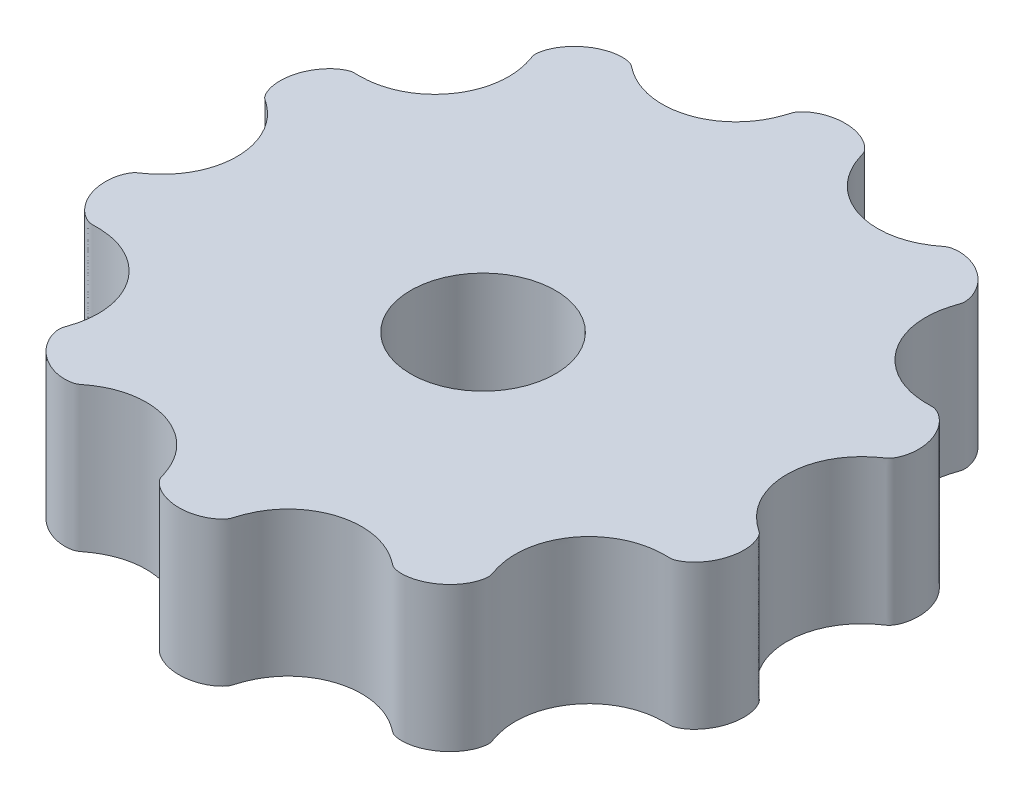
SolidWorks part; units mm, degrees
ref_plane "Front Plane" through (0, 0, 0) normal (0, 0, 1) x (1, 0, 0)
ref_plane "Top Plane" through (0, 0, 0) normal (0, 1, 0) x (1, 0, 0)
ref_plane "Right Plane" through (0, 0, 0) normal (1, 0, 0) x (0, 0, -1)
sketch "Sketch2" plane through (0, 0, 0) normal (0, 1, 0) x (1, 0, 0)
  line L0 (15.6249, 0) -> (-15.6249, 0) construction
  spline S0 degree 4 poles (10.8627, -2.3489) (10.8548, -2.3356) (10.8383, -2.3095) (10.8118, -2.2714) (10.77, -2.2253) (10.7092, -2.1837) (10.6403, -2.1348) (10.5624, -2.0782) (10.4776, -2.012) (10.3744, -1.9255) (10.2561, -1.8157) (10.1267, -1.6784) (9.9922, -1.5103) (9.8721, -1.331) (9.7674, -1.1432) (9.6789, -0.9459) (9.6073, -0.7442) (9.5599, -0.5592) (9.5304, -0.4045) (9.5133, -0.2645) (9.5042, -0.1702) (9.4997, -0.039) (9.4996, 0.0348) (9.5038, 0.1621) (9.5121, 0.2517) (9.5245, 0.3605) (9.5411, 0.4582) (9.5668, 0.5857) (9.6065, 0.7361) (9.6655, 0.9121) (9.75, 1.1075) (9.852, 1.2979) (9.9694, 1.4785) (10.1013, 1.6488) (10.2284, 1.7876) (10.3448, 1.8989) (10.4463, 1.9865) (10.5197, 2.0451) (10.5838, 2.0937) (10.641, 2.1349) (10.6898, 2.1706) (10.7437, 2.2055) (10.7951, 2.2496) (10.8403, 2.311) (10.8841, 2.3827) (10.9343, 2.4894) (11.0002, 2.6876) (11.0407, 2.9778) (11.0115, 3.3556) (10.8743, 3.7728) (10.6723, 4.0946) (10.4644, 4.3047) (10.2934, 4.4229) (10.1936, 4.4756) (10.1202, 4.505) (10.0528, 4.5253) (9.992, 4.5302) (9.9188, 4.5272) (9.8337, 4.5273) (9.7361, 4.5276) (9.6266, 4.5327) (9.5172, 4.5414) (9.4083, 4.5547) (9.2729, 4.5766) (9.1119, 4.6118) (8.9272, 4.666) (8.722, 4.7456) (8.5243, 4.8426) (8.288, 4.9849) (8.0252, 5.1877) (7.758, 5.4641) (7.5129, 5.8251) (7.3343, 6.2184) (7.2385, 6.5803) (7.2002, 6.898) (7.1976, 7.1627) (7.2125, 7.3724) (7.2437, 7.5789) (7.2844, 7.7559) (7.3244, 7.8928) (7.3569, 7.9913) (7.3774, 8.053) (7.3956, 8.102) (7.4112, 8.1658) (7.4126, 8.2693) (7.3936, 8.4084) (7.3248, 8.6324) (7.174, 8.9091) (6.9645, 9.1518) (6.709, 9.3505) (6.4711, 9.4808) (6.2666, 9.5615) (6.0593, 9.6132) (5.8773, 9.6322) (5.725, 9.6284) (5.6081, 9.6108) (5.5203, 9.5887) (5.4392, 9.5544) (5.3742, 9.5002) (5.2792, 9.4314) (5.1556, 9.3435) (4.9977, 9.2467) (4.8029, 9.1463) (4.6002, 9.0629) (4.3912, 8.9964) (4.1772, 8.9481) (3.9597, 8.9181) (3.7403, 8.9069) (3.4104, 8.9186) (3.0342, 8.9868) (2.6266, 9.1359) (2.2143, 9.3876) (1.8947, 9.6642) (1.6607, 9.946) (1.4966, 10.2081) (1.3849, 10.435) (1.3198, 10.5945) (1.2718, 10.7345) (1.2347, 10.8518) (1.2083, 10.949) (1.1472, 11.0306) (1.0807, 11.1054) (1.004, 11.1722) (0.9232, 11.2326) (0.8141, 11.3007) (0.6749, 11.3701) (0.4536, 11.4511) (0.1862, 11.5013) (-0.0944, 11.508) (-0.3799, 11.4665) (-0.6145, 11.3979) (-0.8222, 11.3016) (-0.9804, 11.1957) (-1.0932, 11.0938) (-1.1632, 11.0103) (-1.2092, 10.9408) (-1.2362, 10.8468) (-1.2643, 10.7588) (-1.2935, 10.6703) (-1.3324, 10.5659) (-1.3833, 10.4408) (-1.4592, 10.2808) (-1.5685, 10.0906) (-1.7084, 9.8921) (-1.8668, 9.7071) (-2.0427, 9.5374) (-2.2827, 9.3465) (-2.5882, 9.162) (-2.9131, 9.029) (-3.2473, 8.9481) (-3.5205, 8.9147) (-3.7403, 8.9069) (-3.9597, 8.9181) (-4.1772, 8.9481) (-4.3912, 8.9964) (-4.6002, 9.0629) (-4.8029, 9.1463) (-4.9977, 9.2467) (-5.1556, 9.3435) (-5.2792, 9.4314) (-5.3742, 9.5002) (-5.4392, 9.5544) (-5.5203, 9.5887) (-5.6081, 9.6108) (-5.725, 9.6284) (-5.8773, 9.6322) (-6.0593, 9.6132) (-6.2666, 9.5615) (-6.4711, 9.4808) (-6.7091, 9.3504) (-6.9645, 9.1518) (-7.174, 8.9091) (-7.3247, 8.6324) (-7.3936, 8.4084) (-7.4125, 8.2694) (-7.4114, 8.1658) (-7.3921, 8.0895) (-7.3642, 8.0164) (-7.3286, 7.9051) (-7.2841, 7.756) (-7.2439, 7.5789) (-7.2124, 7.3724) (-7.1976, 7.1627) (-7.2002, 6.898) (-7.2385, 6.5803) (-7.3343, 6.2184) (-7.513, 5.8251) (-7.789, 5.4184) (-8.1046, 5.1102) (-8.425, 4.8913) (-8.722, 4.7456) (-8.9272, 4.666) (-9.1119, 4.6118) (-9.2729, 4.5766) (-9.4083, 4.5547) (-9.5172, 4.5414) (-9.6266, 4.5327) (-9.7361, 4.5276) (-9.8337, 4.5273) (-9.9188, 4.5272) (-9.992, 4.5302) (-10.0528, 4.5253) (-10.1202, 4.5049) (-10.1936, 4.4756) (-10.2934, 4.4228) (-10.419, 4.3361) (-10.5552, 4.2128) (-10.728, 4.006) (-10.8917, 3.72) (-11.0115, 3.3557) (-11.0407, 2.9777) (-11.0002, 2.6876) (-10.9343, 2.4894) (-10.8841, 2.3827) (-10.8403, 2.311) (-10.7951, 2.2496) (-10.7437, 2.2055) (-10.6898, 2.1706) (-10.641, 2.1349) (-10.5838, 2.0937) (-10.5197, 2.0451) (-10.4463, 1.9865) (-10.3448, 1.8989) (-10.2284, 1.7876) (-10.1013, 1.6488) (-9.9694, 1.4785) (-9.852, 1.2979) (-9.75, 1.1075) (-9.6655, 0.912) (-9.5983, 0.7119) (-9.5545, 0.5357) (-9.5276, 0.3828) (-9.5121, 0.2572) (-9.5038, 0.1544) (-9.4985, 0.0087) (-9.5005, -0.0802) (-9.5099, -0.2587) (-9.5304, -0.3927) (-9.5599, -0.5672) (-9.6073, -0.7393) (-9.6789, -0.9488) (-9.7674, -1.1415) (-9.8721, -1.3321) (-9.9922, -1.5096) (-10.1267, -1.6789) (-10.2561, -1.8154) (-10.3744, -1.9257) (-10.4776, -2.0119) (-10.5624, -2.0782) (-10.6403, -2.1347) (-10.7092, -2.1837) (-10.77, -2.2253) (-10.8118, -2.2714) (-10.8383, -2.3095) (-10.8548, -2.3356) (-10.8627, -2.3489) knots 0 0 0 0 0 0.001333 0.002666 0.003999 0.005332 0.007653 0.009974 0.012295 0.014616 0.019258 0.0239 0.028542 0.033183 0.037824 0.042465 0.047106 0.051747 0.054067 0.056388 0.058708 0.061029 0.063242 0.065455 0.067668 0.069881 0.072094 0.074307 0.078733 0.083382 0.08803 0.092679 0.097328 0.101956 0.106583 0.108896 0.11121 0.113524 0.114681 0.115837 0.117292 0.118746 0.1202 0.121654 0.123827 0.126 0.130347 0.13962 0.148891 0.15838 0.167867 0.172067 0.174166 0.176266 0.177578 0.17889 0.180201 0.181513 0.183879 0.186244 0.18861 0.190975 0.193341 0.195706 0.200437 0.205181 0.209925 0.21467 0.219414 0.228944 0.238475 0.24767 0.256866 0.266034 0.270619 0.275203 0.279676 0.284148 0.288621 0.290858 0.291976 0.293094 0.294227 0.29536 0.297625 0.301964 0.306302 0.31546 0.324616 0.329345 0.334073 0.338802 0.34353 0.347716 0.349809 0.351902 0.353711 0.35552 0.357329 0.359138 0.363859 0.368579 0.373299 0.378019 0.382748 0.387476 0.392204 0.396932 0.401678 0.415915 0.425003 0.434092 0.443153 0.452214 0.45646 0.460705 0.464951 0.467074 0.469196 0.471363 0.47353 0.475711 0.477892 0.480073 0.482254 0.486775 0.491297 0.500341 0.505595 0.510849 0.516103 0.521357 0.525258 0.527209 0.52916 0.530763 0.532367 0.535573 0.537176 0.538779 0.541986 0.547215 0.552445 0.557674 0.562903 0.568199 0.573494 0.584085 0.593577 0.598322 0.603068 0.607796 0.612524 0.617252 0.621981 0.626701 0.631421 0.636141 0.640862 0.642671 0.64448 0.646289 0.648098 0.650191 0.652284 0.65647 0.661198 0.665927 0.670655 0.675384 0.68454 0.693698 0.698036 0.702375 0.70464 0.705773 0.706906 0.709142 0.711379 0.715852 0.720324 0.724797 0.729381 0.733966 0.743134 0.75233 0.761525 0.771056 0.78533 0.790075 0.794819 0.799563 0.804294 0.806659 0.809025 0.81139 0.813756 0.816121 0.818487 0.819799 0.82111 0.822422 0.823734 0.825834 0.827933 0.832133 0.836876 0.84162 0.851109 0.86038 0.869653 0.874 0.876173 0.878346 0.8798 0.881254 0.882708 0.884163 0.885319 0.886476 0.88879 0.891104 0.893417 0.898044 0.902672 0.907321 0.91197 0.916618 0.921267 0.925693 0.930119 0.932332 0.934545 0.936758 0.938971 0.943612 0.945933 0.948253 0.952894 0.957535 0.962176 0.966817 0.971458 0.9761 0.980742 0.985384 0.987705 0.990026 0.992347 0.994668 0.996001 0.997334 0.998667 1 1 1 1 1 construction
  spline S1 degree 4 poles (9.5, 0) (9.5, 0.0225) (9.5007, 0.0678) (9.5038, 0.1621) (9.5121, 0.2517) (9.5245, 0.3605) (9.5411, 0.4582) (9.5668, 0.5857) (9.6065, 0.7361) (9.6655, 0.9121) (9.75, 1.1075) (9.852, 1.2979) (9.9694, 1.4785) (10.1013, 1.6488) (10.2284, 1.7876) (10.3448, 1.8989) (10.4463, 1.9865) (10.5197, 2.0451) (10.5838, 2.0937) (10.641, 2.1349) (10.6898, 2.1706) (10.7437, 2.2055) (10.7951, 2.2496) (10.8403, 2.311) (10.8841, 2.3827) (10.9343, 2.4894) (11.0002, 2.6876) (11.0407, 2.9778) (11.0115, 3.3556) (10.8743, 3.7728) (10.6723, 4.0946) (10.4644, 4.3047) (10.2934, 4.4229) (10.1936, 4.4756) (10.1202, 4.505) (10.0528, 4.5253) (9.992, 4.5302) (9.9188, 4.5272) (9.8337, 4.5273) (9.7361, 4.5276) (9.6266, 4.5327) (9.5172, 4.5414) (9.4083, 4.5547) (9.2729, 4.5766) (9.1119, 4.6118) (8.9272, 4.666) (8.722, 4.7456) (8.5243, 4.8426) (8.288, 4.9849) (8.0252, 5.1877) (7.758, 5.4641) (7.5129, 5.8251) (7.3343, 6.2184) (7.2385, 6.5803) (7.2002, 6.898) (7.1976, 7.1627) (7.2125, 7.3724) (7.2437, 7.5789) (7.2844, 7.7559) (7.3244, 7.8928) (7.3569, 7.9913) (7.3774, 8.053) (7.3956, 8.102) (7.4112, 8.1658) (7.4126, 8.2693) (7.3936, 8.4084) (7.3248, 8.6324) (7.174, 8.9091) (6.9645, 9.1518) (6.709, 9.3505) (6.4711, 9.4808) (6.2666, 9.5615) (6.0593, 9.6132) (5.8773, 9.6322) (5.725, 9.6284) (5.6081, 9.6108) (5.5203, 9.5887) (5.4392, 9.5544) (5.3742, 9.5002) (5.2792, 9.4314) (5.1556, 9.3435) (4.9977, 9.2467) (4.8029, 9.1463) (4.6002, 9.0629) (4.3912, 8.9964) (4.1772, 8.9481) (3.9597, 8.9181) (3.7403, 8.9069) (3.4104, 8.9186) (3.0342, 8.9868) (2.6266, 9.1359) (2.2143, 9.3876) (1.8947, 9.6642) (1.6607, 9.946) (1.4966, 10.2081) (1.3849, 10.435) (1.3198, 10.5945) (1.2718, 10.7345) (1.2347, 10.8518) (1.2083, 10.949) (1.1472, 11.0306) (1.0807, 11.1054) (1.004, 11.1722) (0.9232, 11.2326) (0.8141, 11.3007) (0.6749, 11.3701) (0.4536, 11.4511) (0.1862, 11.5013) (-0.0944, 11.508) (-0.3799, 11.4665) (-0.6145, 11.3979) (-0.8222, 11.3016) (-0.9804, 11.1957) (-1.0932, 11.0938) (-1.1632, 11.0103) (-1.2092, 10.9408) (-1.2362, 10.8468) (-1.2643, 10.7588) (-1.2935, 10.6703) (-1.3324, 10.5659) (-1.3833, 10.4408) (-1.4592, 10.2808) (-1.5685, 10.0906) (-1.7084, 9.8921) (-1.8668, 9.7071) (-2.0427, 9.5374) (-2.2827, 9.3465) (-2.5882, 9.162) (-2.9131, 9.029) (-3.2473, 8.9481) (-3.5205, 8.9147) (-3.7403, 8.9069) (-3.9597, 8.9181) (-4.1772, 8.9481) (-4.3912, 8.9964) (-4.6002, 9.0629) (-4.8029, 9.1463) (-4.9977, 9.2467) (-5.1556, 9.3435) (-5.2792, 9.4314) (-5.3742, 9.5002) (-5.4392, 9.5544) (-5.5203, 9.5887) (-5.6081, 9.6108) (-5.725, 9.6284) (-5.8773, 9.6322) (-6.0593, 9.6132) (-6.2666, 9.5615) (-6.4711, 9.4808) (-6.7091, 9.3504) (-6.9645, 9.1518) (-7.174, 8.9091) (-7.3247, 8.6324) (-7.3936, 8.4084) (-7.4125, 8.2694) (-7.4114, 8.1658) (-7.3921, 8.0895) (-7.3642, 8.0164) (-7.3286, 7.9051) (-7.2841, 7.756) (-7.2439, 7.5789) (-7.2124, 7.3724) (-7.1976, 7.1627) (-7.2002, 6.898) (-7.2385, 6.5803) (-7.3343, 6.2184) (-7.513, 5.8251) (-7.789, 5.4184) (-8.1046, 5.1102) (-8.425, 4.8913) (-8.722, 4.7456) (-8.9272, 4.666) (-9.1119, 4.6118) (-9.2729, 4.5766) (-9.4083, 4.5547) (-9.5172, 4.5414) (-9.6266, 4.5327) (-9.7361, 4.5276) (-9.8337, 4.5273) (-9.9188, 4.5272) (-9.992, 4.5302) (-10.0528, 4.5253) (-10.1202, 4.5049) (-10.1936, 4.4756) (-10.2934, 4.4228) (-10.419, 4.3361) (-10.5552, 4.2128) (-10.728, 4.006) (-10.8917, 3.72) (-11.0115, 3.3557) (-11.0407, 2.9777) (-11.0002, 2.6876) (-10.9343, 2.4894) (-10.8841, 2.3827) (-10.8403, 2.311) (-10.7951, 2.2496) (-10.7437, 2.2055) (-10.6898, 2.1706) (-10.641, 2.1349) (-10.5838, 2.0937) (-10.5197, 2.0451) (-10.4463, 1.9865) (-10.3448, 1.8989) (-10.2284, 1.7876) (-10.1013, 1.6488) (-9.9694, 1.4785) (-9.852, 1.2979) (-9.75, 1.1075) (-9.6655, 0.912) (-9.5983, 0.7119) (-9.5545, 0.5357) (-9.5276, 0.3828) (-9.5121, 0.2572) (-9.5038, 0.1544) (-9.5007, 0.0686) (-9.5, 0.0225) (-9.5, 0) knots 0.061029 0.061029 0.061029 0.061029 0.061029 0.063242 0.065455 0.067668 0.069881 0.072094 0.074307 0.078733 0.083382 0.08803 0.092679 0.097328 0.101956 0.106583 0.108896 0.11121 0.113524 0.114681 0.115837 0.117292 0.118746 0.1202 0.121654 0.123827 0.126 0.130347 0.13962 0.148891 0.15838 0.167867 0.172067 0.174166 0.176266 0.177578 0.17889 0.180201 0.181513 0.183879 0.186244 0.18861 0.190975 0.193341 0.195706 0.200437 0.205181 0.209925 0.21467 0.219414 0.228944 0.238475 0.24767 0.256866 0.266034 0.270619 0.275203 0.279676 0.284148 0.288621 0.290858 0.291976 0.293094 0.294227 0.29536 0.297625 0.301964 0.306302 0.31546 0.324616 0.329345 0.334073 0.338802 0.34353 0.347716 0.349809 0.351902 0.353711 0.35552 0.357329 0.359138 0.363859 0.368579 0.373299 0.378019 0.382748 0.387476 0.392204 0.396932 0.401678 0.415915 0.425003 0.434092 0.443153 0.452214 0.45646 0.460705 0.464951 0.467074 0.469196 0.471363 0.47353 0.475711 0.477892 0.480073 0.482254 0.486775 0.491297 0.500341 0.505595 0.510849 0.516103 0.521357 0.525258 0.527209 0.52916 0.530763 0.532367 0.535573 0.537176 0.538779 0.541986 0.547215 0.552445 0.557674 0.562903 0.568199 0.573494 0.584085 0.593577 0.598322 0.603068 0.607796 0.612524 0.617252 0.621981 0.626701 0.631421 0.636141 0.640862 0.642671 0.64448 0.646289 0.648098 0.650191 0.652284 0.65647 0.661198 0.665927 0.670655 0.675384 0.68454 0.693698 0.698036 0.702375 0.70464 0.705773 0.706906 0.709142 0.711379 0.715852 0.720324 0.724797 0.729381 0.733966 0.743134 0.75233 0.761525 0.771056 0.78533 0.790075 0.794819 0.799563 0.804294 0.806659 0.809025 0.81139 0.813756 0.816121 0.818487 0.819799 0.82111 0.822422 0.823734 0.825834 0.827933 0.832133 0.836876 0.84162 0.851109 0.86038 0.869653 0.874 0.876173 0.878346 0.8798 0.881254 0.882708 0.884163 0.885319 0.886476 0.88879 0.891104 0.893417 0.898044 0.902672 0.907321 0.91197 0.916618 0.921267 0.925693 0.930119 0.932332 0.934545 0.936758 0.938971 0.938971 0.938971 0.938971 0.938971 construction
  spline S2 degree 4 poles (10.8627, 2.3489) (10.8548, 2.3356) (10.8383, 2.3095) (10.8118, 2.2714) (10.77, 2.2253) (10.7092, 2.1837) (10.6403, 2.1348) (10.5624, 2.0782) (10.4776, 2.012) (10.3744, 1.9255) (10.2561, 1.8157) (10.1267, 1.6784) (9.9922, 1.5103) (9.8721, 1.331) (9.7674, 1.1432) (9.6789, 0.9459) (9.6073, 0.7442) (9.5599, 0.5592) (9.5304, 0.4045) (9.5133, 0.2645) (9.5042, 0.1702) (9.4997, 0.039) (9.4996, -0.0348) (9.5038, -0.1621) (9.5121, -0.2517) (9.5245, -0.3605) (9.5411, -0.4582) (9.5668, -0.5857) (9.6065, -0.7361) (9.6655, -0.9121) (9.75, -1.1075) (9.852, -1.2979) (9.9694, -1.4785) (10.1013, -1.6488) (10.2284, -1.7876) (10.3448, -1.8989) (10.4463, -1.9865) (10.5197, -2.0451) (10.5838, -2.0937) (10.641, -2.1349) (10.6898, -2.1706) (10.7437, -2.2055) (10.7951, -2.2496) (10.8403, -2.311) (10.8841, -2.3827) (10.9343, -2.4894) (11.0002, -2.6876) (11.0407, -2.9778) (11.0115, -3.3556) (10.8743, -3.7728) (10.6723, -4.0946) (10.4644, -4.3047) (10.2934, -4.4229) (10.1936, -4.4756) (10.1202, -4.505) (10.0528, -4.5253) (9.992, -4.5302) (9.9188, -4.5272) (9.8337, -4.5273) (9.7361, -4.5276) (9.6266, -4.5327) (9.5172, -4.5414) (9.4083, -4.5547) (9.2729, -4.5766) (9.1119, -4.6118) (8.9272, -4.666) (8.722, -4.7456) (8.5243, -4.8426) (8.288, -4.9849) (8.0252, -5.1877) (7.758, -5.4641) (7.5129, -5.8251) (7.3343, -6.2184) (7.2385, -6.5803) (7.2002, -6.898) (7.1976, -7.1627) (7.2125, -7.3724) (7.2437, -7.5789) (7.2844, -7.7559) (7.3244, -7.8928) (7.3569, -7.9913) (7.3774, -8.053) (7.3956, -8.102) (7.4112, -8.1658) (7.4126, -8.2693) (7.3936, -8.4084) (7.3248, -8.6324) (7.174, -8.9091) (6.9645, -9.1518) (6.709, -9.3505) (6.4711, -9.4808) (6.2666, -9.5615) (6.0593, -9.6132) (5.8773, -9.6322) (5.725, -9.6284) (5.6081, -9.6108) (5.5203, -9.5887) (5.4392, -9.5544) (5.3742, -9.5002) (5.2792, -9.4314) (5.1556, -9.3435) (4.9977, -9.2467) (4.8029, -9.1463) (4.6002, -9.0629) (4.3912, -8.9964) (4.1772, -8.9481) (3.9597, -8.9181) (3.7403, -8.9069) (3.4104, -8.9186) (3.0342, -8.9868) (2.6266, -9.1359) (2.2143, -9.3876) (1.8947, -9.6642) (1.6607, -9.946) (1.4966, -10.2081) (1.3849, -10.435) (1.3198, -10.5945) (1.2718, -10.7345) (1.2347, -10.8518) (1.2083, -10.949) (1.1472, -11.0306) (1.0807, -11.1054) (1.004, -11.1722) (0.9232, -11.2326) (0.8141, -11.3007) (0.6749, -11.3701) (0.4536, -11.4511) (0.1862, -11.5013) (-0.0944, -11.508) (-0.3799, -11.4665) (-0.6145, -11.3979) (-0.8222, -11.3016) (-0.9804, -11.1957) (-1.0932, -11.0938) (-1.1632, -11.0103) (-1.2092, -10.9408) (-1.2362, -10.8468) (-1.2643, -10.7588) (-1.2935, -10.6703) (-1.3324, -10.5659) (-1.3833, -10.4408) (-1.4592, -10.2808) (-1.5685, -10.0906) (-1.7084, -9.8921) (-1.8668, -9.7071) (-2.0427, -9.5374) (-2.2827, -9.3465) (-2.5882, -9.162) (-2.9131, -9.029) (-3.2473, -8.9481) (-3.5205, -8.9147) (-3.7403, -8.9069) (-3.9597, -8.9181) (-4.1772, -8.9481) (-4.3912, -8.9964) (-4.6002, -9.0629) (-4.8029, -9.1463) (-4.9977, -9.2467) (-5.1556, -9.3435) (-5.2792, -9.4314) (-5.3742, -9.5002) (-5.4392, -9.5544) (-5.5203, -9.5887) (-5.6081, -9.6108) (-5.725, -9.6284) (-5.8773, -9.6322) (-6.0593, -9.6132) (-6.2666, -9.5615) (-6.4711, -9.4808) (-6.7091, -9.3504) (-6.9645, -9.1518) (-7.174, -8.9091) (-7.3247, -8.6324) (-7.3936, -8.4084) (-7.4125, -8.2694) (-7.4114, -8.1658) (-7.3921, -8.0895) (-7.3642, -8.0164) (-7.3286, -7.9051) (-7.2841, -7.756) (-7.2439, -7.5789) (-7.2124, -7.3724) (-7.1976, -7.1627) (-7.2002, -6.898) (-7.2385, -6.5803) (-7.3343, -6.2184) (-7.513, -5.8251) (-7.789, -5.4184) (-8.1046, -5.1102) (-8.425, -4.8913) (-8.722, -4.7456) (-8.9272, -4.666) (-9.1119, -4.6118) (-9.2729, -4.5766) (-9.4083, -4.5547) (-9.5172, -4.5414) (-9.6266, -4.5327) (-9.7361, -4.5276) (-9.8337, -4.5273) (-9.9188, -4.5272) (-9.992, -4.5302) (-10.0528, -4.5253) (-10.1202, -4.5049) (-10.1936, -4.4756) (-10.2934, -4.4228) (-10.419, -4.3361) (-10.5552, -4.2128) (-10.728, -4.006) (-10.8917, -3.72) (-11.0115, -3.3557) (-11.0407, -2.9777) (-11.0002, -2.6876) (-10.9343, -2.4894) (-10.8841, -2.3827) (-10.8403, -2.311) (-10.7951, -2.2496) (-10.7437, -2.2055) (-10.6898, -2.1706) (-10.641, -2.1349) (-10.5838, -2.0937) (-10.5197, -2.0451) (-10.4463, -1.9865) (-10.3448, -1.8989) (-10.2284, -1.7876) (-10.1013, -1.6488) (-9.9694, -1.4785) (-9.852, -1.2979) (-9.75, -1.1075) (-9.6655, -0.912) (-9.5983, -0.7119) (-9.5545, -0.5357) (-9.5276, -0.3828) (-9.5121, -0.2572) (-9.5038, -0.1544) (-9.4985, -0.0087) (-9.5005, 0.0802) (-9.5099, 0.2587) (-9.5304, 0.3927) (-9.5599, 0.5672) (-9.6073, 0.7393) (-9.6789, 0.9488) (-9.7674, 1.1415) (-9.8721, 1.3321) (-9.9922, 1.5096) (-10.1267, 1.6789) (-10.2561, 1.8154) (-10.3744, 1.9257) (-10.4776, 2.0119) (-10.5624, 2.0782) (-10.6403, 2.1347) (-10.7092, 2.1837) (-10.77, 2.2253) (-10.8118, 2.2714) (-10.8383, 2.3095) (-10.8548, 2.3356) (-10.8627, 2.3489) knots 0 0 0 0 0 0.001333 0.002666 0.003999 0.005332 0.007653 0.009974 0.012295 0.014616 0.019258 0.0239 0.028542 0.033183 0.037824 0.042465 0.047106 0.051747 0.054067 0.056388 0.058708 0.061029 0.063242 0.065455 0.067668 0.069881 0.072094 0.074307 0.078733 0.083382 0.08803 0.092679 0.097328 0.101956 0.106583 0.108896 0.11121 0.113524 0.114681 0.115837 0.117292 0.118746 0.1202 0.121654 0.123827 0.126 0.130347 0.13962 0.148891 0.15838 0.167867 0.172067 0.174166 0.176266 0.177578 0.17889 0.180201 0.181513 0.183879 0.186244 0.18861 0.190975 0.193341 0.195706 0.200437 0.205181 0.209925 0.21467 0.219414 0.228944 0.238475 0.24767 0.256866 0.266034 0.270619 0.275203 0.279676 0.284148 0.288621 0.290858 0.291976 0.293094 0.294227 0.29536 0.297625 0.301964 0.306302 0.31546 0.324616 0.329345 0.334073 0.338802 0.34353 0.347716 0.349809 0.351902 0.353711 0.35552 0.357329 0.359138 0.363859 0.368579 0.373299 0.378019 0.382748 0.387476 0.392204 0.396932 0.401678 0.415915 0.425003 0.434092 0.443153 0.452214 0.45646 0.460705 0.464951 0.467074 0.469196 0.471363 0.47353 0.475711 0.477892 0.480073 0.482254 0.486775 0.491297 0.500341 0.505595 0.510849 0.516103 0.521357 0.525258 0.527209 0.52916 0.530763 0.532367 0.535573 0.537176 0.538779 0.541986 0.547215 0.552445 0.557674 0.562903 0.568199 0.573494 0.584085 0.593577 0.598322 0.603068 0.607796 0.612524 0.617252 0.621981 0.626701 0.631421 0.636141 0.640862 0.642671 0.64448 0.646289 0.648098 0.650191 0.652284 0.65647 0.661198 0.665927 0.670655 0.675384 0.68454 0.693698 0.698036 0.702375 0.70464 0.705773 0.706906 0.709142 0.711379 0.715852 0.720324 0.724797 0.729381 0.733966 0.743134 0.75233 0.761525 0.771056 0.78533 0.790075 0.794819 0.799563 0.804294 0.806659 0.809025 0.81139 0.813756 0.816121 0.818487 0.819799 0.82111 0.822422 0.823734 0.825834 0.827933 0.832133 0.836876 0.84162 0.851109 0.86038 0.869653 0.874 0.876173 0.878346 0.8798 0.881254 0.882708 0.884163 0.885319 0.886476 0.88879 0.891104 0.893417 0.898044 0.902672 0.907321 0.91197 0.916618 0.921267 0.925693 0.930119 0.932332 0.934545 0.936758 0.938971 0.943612 0.945933 0.948253 0.952894 0.957535 0.962176 0.966817 0.971458 0.9761 0.980742 0.985384 0.987705 0.990026 0.992347 0.994668 0.996001 0.997334 0.998667 1 1 1 1 1 construction
  spline S3 degree 4 poles (9.5, 0) (9.5, -0.0225) (9.5007, -0.0678) (9.5038, -0.1621) (9.5121, -0.2517) (9.5245, -0.3605) (9.5411, -0.4582) (9.5668, -0.5857) (9.6065, -0.7361) (9.6655, -0.9121) (9.75, -1.1075) (9.852, -1.2979) (9.9694, -1.4785) (10.1013, -1.6488) (10.2284, -1.7876) (10.3448, -1.8989) (10.4463, -1.9865) (10.5197, -2.0451) (10.5838, -2.0937) (10.641, -2.1349) (10.6898, -2.1706) (10.7437, -2.2055) (10.7951, -2.2496) (10.8403, -2.311) (10.8841, -2.3827) (10.9343, -2.4894) (11.0002, -2.6876) (11.0407, -2.9778) (11.0115, -3.3556) (10.8743, -3.7728) (10.6723, -4.0946) (10.4644, -4.3047) (10.2934, -4.4229) (10.1936, -4.4756) (10.1202, -4.505) (10.0528, -4.5253) (9.992, -4.5302) (9.9188, -4.5272) (9.8337, -4.5273) (9.7361, -4.5276) (9.6266, -4.5327) (9.5172, -4.5414) (9.4083, -4.5547) (9.2729, -4.5766) (9.1119, -4.6118) (8.9272, -4.666) (8.722, -4.7456) (8.5243, -4.8426) (8.288, -4.9849) (8.0252, -5.1877) (7.758, -5.4641) (7.5129, -5.8251) (7.3343, -6.2184) (7.2385, -6.5803) (7.2002, -6.898) (7.1976, -7.1627) (7.2125, -7.3724) (7.2437, -7.5789) (7.2844, -7.7559) (7.3244, -7.8928) (7.3569, -7.9913) (7.3774, -8.053) (7.3956, -8.102) (7.4112, -8.1658) (7.4126, -8.2693) (7.3936, -8.4084) (7.3248, -8.6324) (7.174, -8.9091) (6.9645, -9.1518) (6.709, -9.3505) (6.4711, -9.4808) (6.2666, -9.5615) (6.0593, -9.6132) (5.8773, -9.6322) (5.725, -9.6284) (5.6081, -9.6108) (5.5203, -9.5887) (5.4392, -9.5544) (5.3742, -9.5002) (5.2792, -9.4314) (5.1556, -9.3435) (4.9977, -9.2467) (4.8029, -9.1463) (4.6002, -9.0629) (4.3912, -8.9964) (4.1772, -8.9481) (3.9597, -8.9181) (3.7403, -8.9069) (3.4104, -8.9186) (3.0342, -8.9868) (2.6266, -9.1359) (2.2143, -9.3876) (1.8947, -9.6642) (1.6607, -9.946) (1.4966, -10.2081) (1.3849, -10.435) (1.3198, -10.5945) (1.2718, -10.7345) (1.2347, -10.8518) (1.2083, -10.949) (1.1472, -11.0306) (1.0807, -11.1054) (1.004, -11.1722) (0.9232, -11.2326) (0.8141, -11.3007) (0.6749, -11.3701) (0.4536, -11.4511) (0.1862, -11.5013) (-0.0944, -11.508) (-0.3799, -11.4665) (-0.6145, -11.3979) (-0.8222, -11.3016) (-0.9804, -11.1957) (-1.0932, -11.0938) (-1.1632, -11.0103) (-1.2092, -10.9408) (-1.2362, -10.8468) (-1.2643, -10.7588) (-1.2935, -10.6703) (-1.3324, -10.5659) (-1.3833, -10.4408) (-1.4592, -10.2808) (-1.5685, -10.0906) (-1.7084, -9.8921) (-1.8668, -9.7071) (-2.0427, -9.5374) (-2.2827, -9.3465) (-2.5882, -9.162) (-2.9131, -9.029) (-3.2473, -8.9481) (-3.5205, -8.9147) (-3.7403, -8.9069) (-3.9597, -8.9181) (-4.1772, -8.9481) (-4.3912, -8.9964) (-4.6002, -9.0629) (-4.8029, -9.1463) (-4.9977, -9.2467) (-5.1556, -9.3435) (-5.2792, -9.4314) (-5.3742, -9.5002) (-5.4392, -9.5544) (-5.5203, -9.5887) (-5.6081, -9.6108) (-5.725, -9.6284) (-5.8773, -9.6322) (-6.0593, -9.6132) (-6.2666, -9.5615) (-6.4711, -9.4808) (-6.7091, -9.3504) (-6.9645, -9.1518) (-7.174, -8.9091) (-7.3247, -8.6324) (-7.3936, -8.4084) (-7.4125, -8.2694) (-7.4114, -8.1658) (-7.3921, -8.0895) (-7.3642, -8.0164) (-7.3286, -7.9051) (-7.2841, -7.756) (-7.2439, -7.5789) (-7.2124, -7.3724) (-7.1976, -7.1627) (-7.2002, -6.898) (-7.2385, -6.5803) (-7.3343, -6.2184) (-7.513, -5.8251) (-7.789, -5.4184) (-8.1046, -5.1102) (-8.425, -4.8913) (-8.722, -4.7456) (-8.9272, -4.666) (-9.1119, -4.6118) (-9.2729, -4.5766) (-9.4083, -4.5547) (-9.5172, -4.5414) (-9.6266, -4.5327) (-9.7361, -4.5276) (-9.8337, -4.5273) (-9.9188, -4.5272) (-9.992, -4.5302) (-10.0528, -4.5253) (-10.1202, -4.5049) (-10.1936, -4.4756) (-10.2934, -4.4228) (-10.419, -4.3361) (-10.5552, -4.2128) (-10.728, -4.006) (-10.8917, -3.72) (-11.0115, -3.3557) (-11.0407, -2.9777) (-11.0002, -2.6876) (-10.9343, -2.4894) (-10.8841, -2.3827) (-10.8403, -2.311) (-10.7951, -2.2496) (-10.7437, -2.2055) (-10.6898, -2.1706) (-10.641, -2.1349) (-10.5838, -2.0937) (-10.5197, -2.0451) (-10.4463, -1.9865) (-10.3448, -1.8989) (-10.2284, -1.7876) (-10.1013, -1.6488) (-9.9694, -1.4785) (-9.852, -1.2979) (-9.75, -1.1075) (-9.6655, -0.912) (-9.5983, -0.7119) (-9.5545, -0.5357) (-9.5276, -0.3828) (-9.5121, -0.2572) (-9.5038, -0.1544) (-9.5007, -0.0686) (-9.5, -0.0225) (-9.5, 0) knots 0.061029 0.061029 0.061029 0.061029 0.061029 0.063242 0.065455 0.067668 0.069881 0.072094 0.074307 0.078733 0.083382 0.08803 0.092679 0.097328 0.101956 0.106583 0.108896 0.11121 0.113524 0.114681 0.115837 0.117292 0.118746 0.1202 0.121654 0.123827 0.126 0.130347 0.13962 0.148891 0.15838 0.167867 0.172067 0.174166 0.176266 0.177578 0.17889 0.180201 0.181513 0.183879 0.186244 0.18861 0.190975 0.193341 0.195706 0.200437 0.205181 0.209925 0.21467 0.219414 0.228944 0.238475 0.24767 0.256866 0.266034 0.270619 0.275203 0.279676 0.284148 0.288621 0.290858 0.291976 0.293094 0.294227 0.29536 0.297625 0.301964 0.306302 0.31546 0.324616 0.329345 0.334073 0.338802 0.34353 0.347716 0.349809 0.351902 0.353711 0.35552 0.357329 0.359138 0.363859 0.368579 0.373299 0.378019 0.382748 0.387476 0.392204 0.396932 0.401678 0.415915 0.425003 0.434092 0.443153 0.452214 0.45646 0.460705 0.464951 0.467074 0.469196 0.471363 0.47353 0.475711 0.477892 0.480073 0.482254 0.486775 0.491297 0.500341 0.505595 0.510849 0.516103 0.521357 0.525258 0.527209 0.52916 0.530763 0.532367 0.535573 0.537176 0.538779 0.541986 0.547215 0.552445 0.557674 0.562903 0.568199 0.573494 0.584085 0.593577 0.598322 0.603068 0.607796 0.612524 0.617252 0.621981 0.626701 0.631421 0.636141 0.640862 0.642671 0.64448 0.646289 0.648098 0.650191 0.652284 0.65647 0.661198 0.665927 0.670655 0.675384 0.68454 0.693698 0.698036 0.702375 0.70464 0.705773 0.706906 0.709142 0.711379 0.715852 0.720324 0.724797 0.729381 0.733966 0.743134 0.75233 0.761525 0.771056 0.78533 0.790075 0.794819 0.799563 0.804294 0.806659 0.809025 0.81139 0.813756 0.816121 0.818487 0.819799 0.82111 0.822422 0.823734 0.825834 0.827933 0.832133 0.836876 0.84162 0.851109 0.86038 0.869653 0.874 0.876173 0.878346 0.8798 0.881254 0.882708 0.884163 0.885319 0.886476 0.88879 0.891104 0.893417 0.898044 0.902672 0.907321 0.91197 0.916618 0.921267 0.925693 0.930119 0.932332 0.934545 0.936758 0.938971 0.938971 0.938971 0.938971 0.938971 construction
  spline S4 degree 4 poles (9.5, 0) (9.5, 0.0225) (9.5007, 0.0678) (9.5038, 0.1621) (9.5121, 0.2517) (9.5245, 0.3605) (9.5411, 0.4582) (9.5668, 0.5857) (9.6065, 0.7361) (9.6655, 0.9121) (9.75, 1.1075) (9.852, 1.2979) (9.9694, 1.4785) (10.1013, 1.6488) (10.2284, 1.7876) (10.3448, 1.8989) (10.4463, 1.9865) (10.5197, 2.0451) (10.5838, 2.0937) (10.641, 2.1349) (10.6898, 2.1706) (10.7437, 2.2055) (10.7951, 2.2496) (10.8403, 2.311) (10.8841, 2.3827) (10.9343, 2.4894) (11.0002, 2.6876) (11.0407, 2.9778) (11.0115, 3.3556) (10.8743, 3.7728) (10.6723, 4.0946) (10.4644, 4.3047) (10.2934, 4.4229) (10.1936, 4.4756) (10.1202, 4.505) (10.0528, 4.5253) (9.992, 4.5302) (9.9188, 4.5272) (9.8337, 4.5273) (9.7361, 4.5276) (9.6266, 4.5327) (9.5172, 4.5414) (9.4083, 4.5547) (9.2729, 4.5766) (9.1119, 4.6118) (8.9272, 4.666) (8.722, 4.7456) (8.5243, 4.8426) (8.288, 4.9849) (8.0252, 5.1877) (7.758, 5.4641) (7.5129, 5.8251) (7.3343, 6.2184) (7.2385, 6.5803) (7.2002, 6.898) (7.1976, 7.1627) (7.2125, 7.3724) (7.2437, 7.5789) (7.2844, 7.7559) (7.3244, 7.8928) (7.3569, 7.9913) (7.3774, 8.053) (7.3956, 8.102) (7.4112, 8.1658) (7.4126, 8.2693) (7.3936, 8.4084) (7.3248, 8.6324) (7.174, 8.9091) (6.9645, 9.1518) (6.709, 9.3505) (6.4711, 9.4808) (6.2666, 9.5615) (6.0593, 9.6132) (5.8773, 9.6322) (5.725, 9.6284) (5.6081, 9.6108) (5.5203, 9.5887) (5.4392, 9.5544) (5.3742, 9.5002) (5.2792, 9.4314) (5.1556, 9.3435) (4.9977, 9.2467) (4.8029, 9.1463) (4.6002, 9.0629) (4.3912, 8.9964) (4.1772, 8.9481) (3.9597, 8.9181) (3.7403, 8.9069) (3.4104, 8.9186) (3.0342, 8.9868) (2.6266, 9.1359) (2.2143, 9.3876) (1.8947, 9.6642) (1.6607, 9.946) (1.4966, 10.2081) (1.3849, 10.435) (1.3198, 10.5945) (1.2718, 10.7345) (1.2347, 10.8518) (1.2083, 10.949) (1.1472, 11.0306) (1.0807, 11.1054) (1.004, 11.1722) (0.9232, 11.2326) (0.8141, 11.3007) (0.6749, 11.3701) (0.4536, 11.4511) (0.1862, 11.5013) (-0.0944, 11.508) (-0.3799, 11.4665) (-0.6145, 11.3979) (-0.8222, 11.3016) (-0.9804, 11.1957) (-1.0932, 11.0938) (-1.1632, 11.0103) (-1.2092, 10.9408) (-1.2362, 10.8468) (-1.2643, 10.7588) (-1.2935, 10.6703) (-1.3324, 10.5659) (-1.3833, 10.4408) (-1.4592, 10.2808) (-1.5685, 10.0906) (-1.7084, 9.8921) (-1.8668, 9.7071) (-2.0427, 9.5374) (-2.2827, 9.3465) (-2.5882, 9.162) (-2.9131, 9.029) (-3.2473, 8.9481) (-3.5205, 8.9147) (-3.7403, 8.9069) (-3.9597, 8.9181) (-4.1772, 8.9481) (-4.3912, 8.9964) (-4.6002, 9.0629) (-4.8029, 9.1463) (-4.9977, 9.2467) (-5.1556, 9.3435) (-5.2792, 9.4314) (-5.3742, 9.5002) (-5.4392, 9.5544) (-5.5203, 9.5887) (-5.6081, 9.6108) (-5.725, 9.6284) (-5.8773, 9.6322) (-6.0593, 9.6132) (-6.2666, 9.5615) (-6.4711, 9.4808) (-6.7091, 9.3504) (-6.9645, 9.1518) (-7.174, 8.9091) (-7.3247, 8.6324) (-7.3936, 8.4084) (-7.4125, 8.2694) (-7.4114, 8.1658) (-7.3921, 8.0895) (-7.3642, 8.0164) (-7.3286, 7.9051) (-7.2841, 7.756) (-7.2439, 7.5789) (-7.2124, 7.3724) (-7.1976, 7.1627) (-7.2002, 6.898) (-7.2385, 6.5803) (-7.3343, 6.2184) (-7.513, 5.8251) (-7.789, 5.4184) (-8.1046, 5.1102) (-8.425, 4.8913) (-8.722, 4.7456) (-8.9272, 4.666) (-9.1119, 4.6118) (-9.2729, 4.5766) (-9.4083, 4.5547) (-9.5172, 4.5414) (-9.6266, 4.5327) (-9.7361, 4.5276) (-9.8337, 4.5273) (-9.9188, 4.5272) (-9.992, 4.5302) (-10.0528, 4.5253) (-10.1202, 4.5049) (-10.1936, 4.4756) (-10.2934, 4.4228) (-10.419, 4.3361) (-10.5552, 4.2128) (-10.728, 4.006) (-10.8917, 3.72) (-11.0115, 3.3557) (-11.0407, 2.9777) (-11.0002, 2.6876) (-10.9343, 2.4894) (-10.8841, 2.3827) (-10.8403, 2.311) (-10.7951, 2.2496) (-10.7437, 2.2055) (-10.6898, 2.1706) (-10.641, 2.1349) (-10.5838, 2.0937) (-10.5197, 2.0451) (-10.4463, 1.9865) (-10.3448, 1.8989) (-10.2284, 1.7876) (-10.1013, 1.6488) (-9.9694, 1.4785) (-9.852, 1.2979) (-9.75, 1.1075) (-9.6655, 0.912) (-9.5983, 0.7119) (-9.5545, 0.5357) (-9.5276, 0.3828) (-9.5121, 0.2572) (-9.5038, 0.1544) (-9.5007, 0.0686) (-9.5, 0.0225) (-9.5, 0) (-9.5, -0.0225) (-9.5007, -0.0686) (-9.5038, -0.1544) (-9.5121, -0.2572) (-9.5276, -0.3828) (-9.5545, -0.5357) (-9.5983, -0.7119) (-9.6655, -0.912) (-9.75, -1.1075) (-9.852, -1.2979) (-9.9694, -1.4785) (-10.1013, -1.6488) (-10.2284, -1.7876) (-10.3448, -1.8989) (-10.4463, -1.9865) (-10.5197, -2.0451) (-10.5838, -2.0937) (-10.641, -2.1349) (-10.6898, -2.1706) (-10.7437, -2.2055) (-10.7951, -2.2496) (-10.8403, -2.311) (-10.8841, -2.3827) (-10.9343, -2.4894) (-11.0002, -2.6876) (-11.0407, -2.9777) (-11.0115, -3.3557) (-10.8917, -3.72) (-10.728, -4.006) (-10.5552, -4.2128) (-10.419, -4.3361) (-10.2934, -4.4228) (-10.1936, -4.4756) (-10.1202, -4.5049) (-10.0528, -4.5253) (-9.992, -4.5302) (-9.9188, -4.5272) (-9.8337, -4.5273) (-9.7361, -4.5276) (-9.6266, -4.5327) (-9.5172, -4.5414) (-9.4083, -4.5547) (-9.2729, -4.5766) (-9.1119, -4.6118) (-8.9272, -4.666) (-8.722, -4.7456) (-8.425, -4.8913) (-8.1046, -5.1102) (-7.789, -5.4184) (-7.513, -5.8251) (-7.3343, -6.2184) (-7.2385, -6.5803) (-7.2002, -6.898) (-7.1976, -7.1627) (-7.2124, -7.3724) (-7.2439, -7.5789) (-7.2841, -7.756) (-7.3286, -7.9051) (-7.3642, -8.0164) (-7.3921, -8.0895) (-7.4114, -8.1658) (-7.4125, -8.2694) (-7.3936, -8.4084) (-7.3247, -8.6324) (-7.174, -8.9091) (-6.9645, -9.1518) (-6.7091, -9.3504) (-6.4711, -9.4808) (-6.2666, -9.5615) (-6.0593, -9.6132) (-5.8773, -9.6322) (-5.725, -9.6284) (-5.6081, -9.6108) (-5.5203, -9.5887) (-5.4392, -9.5544) (-5.3742, -9.5002) (-5.2792, -9.4314) (-5.1556, -9.3435) (-4.9977, -9.2467) (-4.8029, -9.1463) (-4.6002, -9.0629) (-4.3912, -8.9964) (-4.1772, -8.9481) (-3.9597, -8.9181) (-3.7403, -8.9069) (-3.5205, -8.9147) (-3.2473, -8.9481) (-2.9131, -9.029) (-2.5882, -9.162) (-2.2827, -9.3465) (-2.0427, -9.5374) (-1.8668, -9.7071) (-1.7084, -9.8921) (-1.5685, -10.0906) (-1.4592, -10.2808) (-1.3833, -10.4408) (-1.3324, -10.5659) (-1.2935, -10.6703) (-1.2643, -10.7588) (-1.2362, -10.8468) (-1.2092, -10.9408) (-1.1632, -11.0103) (-1.0932, -11.0938) (-0.9804, -11.1957) (-0.8222, -11.3016) (-0.6145, -11.3979) (-0.3799, -11.4665) (-0.0944, -11.508) (0.1862, -11.5013) (0.4536, -11.4511) (0.6749, -11.3701) (0.8141, -11.3007) (0.9232, -11.2326) (1.004, -11.1722) (1.0807, -11.1054) (1.1472, -11.0306) (1.2083, -10.949) (1.2347, -10.8518) (1.2718, -10.7345) (1.3198, -10.5945) (1.3849, -10.435) (1.4966, -10.2081) (1.6607, -9.946) (1.8947, -9.6642) (2.2143, -9.3876) (2.6266, -9.1359) (3.0342, -8.9868) (3.4104, -8.9186) (3.7403, -8.9069) (3.9597, -8.9181) (4.1772, -8.9481) (4.3912, -8.9964) (4.6002, -9.0629) (4.8029, -9.1463) (4.9977, -9.2467) (5.1556, -9.3435) (5.2792, -9.4314) (5.3742, -9.5002) (5.4392, -9.5544) (5.5203, -9.5887) (5.6081, -9.6108) (5.725, -9.6284) (5.8773, -9.6322) (6.0593, -9.6132) (6.2666, -9.5615) (6.4711, -9.4808) (6.709, -9.3505) (6.9645, -9.1518) (7.174, -8.9091) (7.3248, -8.6324) (7.3936, -8.4084) (7.4126, -8.2693) (7.4112, -8.1658) (7.3956, -8.102) (7.3774, -8.053) (7.3569, -7.9913) (7.3244, -7.8928) (7.2844, -7.7559) (7.2437, -7.5789) (7.2125, -7.3724) (7.1976, -7.1627) (7.2002, -6.898) (7.2385, -6.5803) (7.3343, -6.2184) (7.5129, -5.8251) (7.758, -5.4641) (8.0252, -5.1877) (8.288, -4.9849) (8.5243, -4.8426) (8.722, -4.7456) (8.9272, -4.666) (9.1119, -4.6118) (9.2729, -4.5766) (9.4083, -4.5547) (9.5172, -4.5414) (9.6266, -4.5327) (9.7361, -4.5276) (9.8337, -4.5273) (9.9188, -4.5272) (9.992, -4.5302) (10.0528, -4.5253) (10.1202, -4.505) (10.1936, -4.4756) (10.2934, -4.4229) (10.4644, -4.3047) (10.6723, -4.0946) (10.8743, -3.7728) (11.0115, -3.3556) (11.0407, -2.9778) (11.0002, -2.6876) (10.9343, -2.4894) (10.8841, -2.3827) (10.8403, -2.311) (10.7951, -2.2496) (10.7437, -2.2055) (10.6898, -2.1706) (10.641, -2.1349) (10.5838, -2.0937) (10.5197, -2.0451) (10.4463, -1.9865) (10.3448, -1.8989) (10.2284, -1.7876) (10.1013, -1.6488) (9.9694, -1.4785) (9.852, -1.2979) (9.75, -1.1075) (9.6655, -0.9121) (9.6065, -0.7361) (9.5668, -0.5857) (9.5411, -0.4582) (9.5245, -0.3605) (9.5121, -0.2517) (9.5038, -0.1621) (9.5007, -0.0678) (9.5, -0.0225) (9.5, 0) (9.5, 0.0225) (9.5007, 0.0678) (9.5038, 0.1621) knots -0.00126 0 0 0 0 0.00126 0.002521 0.003781 0.005041 0.006302 0.007562 0.010083 0.01273 0.015378 0.018025 0.020673 0.023308 0.025944 0.027261 0.028579 0.029897 0.030555 0.031214 0.032042 0.032871 0.033699 0.034527 0.035765 0.037002 0.039477 0.044759 0.050039 0.055443 0.060846 0.063238 0.064433 0.065629 0.066376 0.067123 0.06787 0.068618 0.069965 0.071312 0.072659 0.074006 0.075353 0.076701 0.079395 0.082097 0.084799 0.087501 0.090202 0.09563 0.101058 0.106295 0.111532 0.116753 0.119364 0.121975 0.124522 0.12707 0.129617 0.130891 0.131528 0.132164 0.132809 0.133455 0.134745 0.137216 0.139687 0.144902 0.150116 0.152809 0.155503 0.158195 0.160888 0.163272 0.164464 0.165656 0.166686 0.167717 0.168747 0.169777 0.172466 0.175154 0.177842 0.18053 0.183223 0.185916 0.188609 0.191301 0.194004 0.202112 0.207288 0.212464 0.217625 0.222785 0.225203 0.227621 0.230039 0.231248 0.232457 0.233691 0.234925 0.236167 0.237409 0.238651 0.239893 0.242468 0.245044 0.250194 0.253186 0.256179 0.259171 0.262163 0.264385 0.265496 0.266607 0.26752 0.268433 0.270259 0.271172 0.272085 0.273911 0.27689 0.279868 0.282846 0.285824 0.28884 0.291856 0.297888 0.303293 0.305996 0.308699 0.311391 0.314084 0.316777 0.31947 0.322158 0.324846 0.327534 0.330223 0.331253 0.332283 0.333314 0.334344 0.335536 0.336728 0.339112 0.341805 0.344497 0.347191 0.349884 0.355098 0.360313 0.362784 0.365255 0.366545 0.367191 0.367836 0.369109 0.370383 0.37293 0.375478 0.378025 0.380636 0.383247 0.388468 0.393705 0.398942 0.40437 0.412499 0.415201 0.417903 0.420605 0.423299 0.424647 0.425994 0.427341 0.428688 0.430035 0.431382 0.43213 0.432877 0.433624 0.434371 0.435567 0.436762 0.439154 0.441856 0.444557 0.449961 0.455241 0.460523 0.462998 0.464235 0.465473 0.466301 0.467129 0.467958 0.468786 0.469445 0.470103 0.471421 0.472739 0.474056 0.476692 0.479327 0.481975 0.484622 0.48727 0.489917 0.492438 0.494959 0.496219 0.497479 0.49874 0.5 0.5 0.5 0.5 0.50126 0.502521 0.503781 0.505041 0.507562 0.510083 0.51273 0.515378 0.518025 0.520673 0.523308 0.525944 0.527261 0.528579 0.529897 0.530555 0.531214 0.532042 0.532871 0.533699 0.534527 0.535765 0.537002 0.539477 0.544759 0.550039 0.555443 0.558144 0.560846 0.563238 0.564433 0.565629 0.566376 0.567123 0.56787 0.568618 0.569965 0.571312 0.572659 0.574006 0.575353 0.576701 0.579395 0.582097 0.584799 0.587501 0.59563 0.601058 0.606295 0.611532 0.616753 0.619364 0.621975 0.624522 0.62707 0.629617 0.630891 0.632164 0.632809 0.633455 0.634745 0.637216 0.639687 0.644902 0.650116 0.652809 0.655503 0.658195 0.660888 0.663272 0.664464 0.665656 0.666686 0.667717 0.668747 0.669777 0.672466 0.675154 0.677842 0.68053 0.683223 0.685916 0.688609 0.691301 0.694004 0.696707 0.702112 0.708144 0.71116 0.714176 0.717154 0.720132 0.72311 0.726089 0.727915 0.728828 0.729741 0.731567 0.73248 0.733393 0.734504 0.735615 0.737837 0.740829 0.743821 0.746814 0.749806 0.754956 0.757532 0.760107 0.761349 0.762591 0.763833 0.765075 0.766309 0.767543 0.768752 0.769961 0.772379 0.774797 0.777215 0.782375 0.787536 0.792712 0.797888 0.805996 0.808699 0.811391 0.814084 0.816777 0.81947 0.822158 0.824846 0.827534 0.830223 0.831253 0.832283 0.833314 0.834344 0.835536 0.836728 0.839112 0.841805 0.844497 0.847191 0.849884 0.855098 0.860313 0.862784 0.865255 0.866545 0.867191 0.867836 0.868472 0.869109 0.870383 0.87293 0.875478 0.878025 0.880636 0.883247 0.888468 0.893705 0.898942 0.90437 0.909798 0.912499 0.915201 0.917903 0.920605 0.923299 0.924647 0.925994 0.927341 0.928688 0.930035 0.931382 0.93213 0.932877 0.933624 0.934371 0.935567 0.936762 0.939154 0.944557 0.949961 0.955241 0.960523 0.962998 0.964235 0.965473 0.966301 0.967129 0.967958 0.968786 0.969445 0.970103 0.971421 0.972739 0.974056 0.976692 0.979327 0.981975 0.984622 0.98727 0.989917 0.992438 0.993698 0.994959 0.996219 0.997479 0.99874 1 1 1 1 1.00126 1.002521 1.003781 1.005041 only from (9.5, 0) to (9.5, 0)
extrude "Boss-Extrude1" add sketch "Sketch2" along normal blind 5 contours S4
sketch "Sketch3" plane through (0, 5, 0) normal (0, 1, 0) x (1, 0, 0)
  circle A0 centre (0, -1) radius 2.5
  dimension "D1" = 5
  dimension "D2" = 1
extrude "Cut-Extrude1" cut sketch "Sketch3" against normal through all
